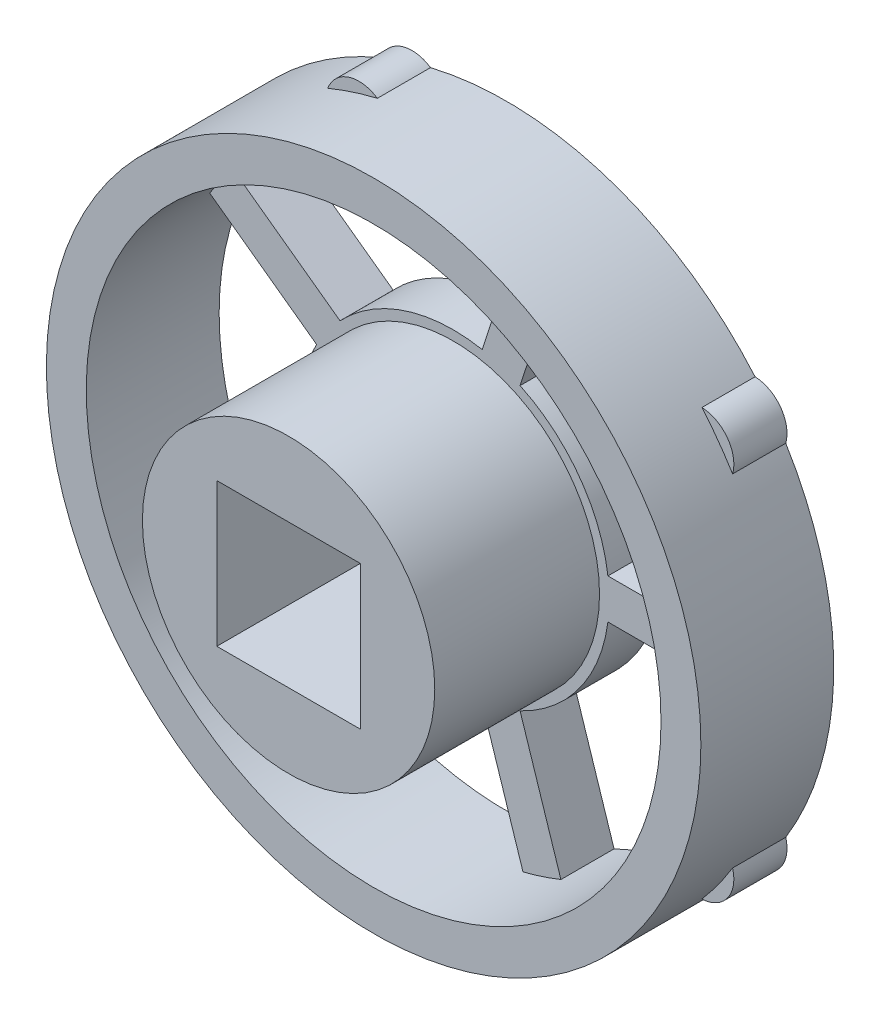
SolidWorks part; units mm, degrees
ref_plane "정면" through (0, 0, 0) normal (1, 0, 0) x (0, 1, 0)
ref_plane "윗면" through (0, 0, 0) normal (0, 0, 1) x (0, 1, 0)
ref_plane "우측면" through (0, 0, 0) normal (0, 1, 0) x (-1, 0, 0)
sketch "스케치1" plane through (0, 0, 0) normal (0, 0, 1) x (0, 1, 0)
  line L0 (0, 0) -> (0, 10.25) construction
  line L1 (-2.7, 2.7) -> (2.7, 2.7)
  line L2 (-2.7, 2.7) -> (-2.7, -2.7)
  line L3 (-2.7, -2.7) -> (2.7, -2.7)
  line L4 (2.7, 2.7) -> (2.7, -2.7)
  line L5 (-2.7, 2.7) -> (2.7, -2.7) construction
  line L6 (-2.7, -2.7) -> (2.7, 2.7) construction
  line L7 (0, 12.3131) -> (0, 16.9922) construction
  line L8 (0, 0) -> (0, -2.7) construction
  line L11 (-0.75, -5.8152) -> (-0.75, -10.787)
  line L13 (0.75, -5.8152) -> (0.75, -10.787)
  line L14 (-0.5407, -5.8384) -> (0.6261, -10.7949) construction
  line L15 (-0.6261, -10.7949) -> (0.5407, -5.8384) construction
  line L16 (-5.7623, -1.0837) -> (-10.4908, -2.6201)
  line L18 (-5.2988, -2.5103) -> (-10.0273, -4.0467)
  line L20 (-2.8113, 5.1454) -> (-5.7337, 9.1677)
  line L22 (-4.0249, 4.2638) -> (-6.9472, 8.2861)
  line L24 (4.0249, 4.2638) -> (6.9472, 8.2861)
  line L26 (2.8113, 5.1454) -> (5.7337, 9.1677)
  line L28 (5.2988, -2.5103) -> (10.0273, -4.0467)
  line L30 (5.7623, -1.0837) -> (10.4908, -2.6201)
  line L34 (0, -11.3212) -> (0, -13.9361) construction
  line L39 (0, -4.9492) -> (0, -8.1352) construction
  arc A0 (5.7623, -1.0837) -> (4.0249, 4.2638) centre (0, 0) ccw
  arc A1 (-11.9765, 2.8592) -> (-8.0086, -9.3528) centre (0, 0) ccw
  arc A2 (0.9816, 12.2739) -> (-0.9816, 12.2739) centre (0, 11.5) ccw
  arc A3 (-11.9765, 2.8592) -> (-8.0086, -9.3528) centre (0, 0) ccw
  arc A4 (-11.3698, 4.7264) -> (-11.9765, 2.8592) centre (-10.9371, 3.5537) ccw
  arc A5 (-11.9765, 2.8592) -> (-8.0086, -9.3528) centre (0, 0) ccw
  arc A6 (-8.0086, -9.3528) -> (-6.4202, -10.5068) centre (-6.7595, -9.3037) ccw
  arc A7 (-11.9765, 2.8592) -> (-8.0086, -9.3528) centre (0, 0) ccw
  arc A8 (6.4202, -10.5068) -> (8.0086, -9.3528) centre (6.7595, -9.3037) ccw
  arc A9 (-11.9765, 2.8592) -> (-8.0086, -9.3528) centre (0, 0) ccw
  arc A10 (11.9765, 2.8592) -> (11.3698, 4.7264) centre (10.9371, 3.5537) ccw
  arc A11 (-6.9472, 8.2861) -> (-10.4908, -2.6201) centre (0, 0) ccw
  circle A12 centre (0, 0) radius 12.3131 construction
  arc A13 (-6.4202, -10.5068) -> (6.4202, -10.5068) centre (0, 0) ccw
  arc A14 (-6.4202, -10.5068) -> (6.4202, -10.5068) centre (0, 0) ccw
  arc A15 (-6.4202, -10.5068) -> (6.4202, -10.5068) centre (0, 0) ccw
  arc A16 (-6.4202, -10.5068) -> (6.4202, -10.5068) centre (0, 0) ccw
  arc A17 (-6.4202, -10.5068) -> (6.4202, -10.5068) centre (0, 0) ccw
  arc A18 (8.0086, -9.3528) -> (11.9765, 2.8592) centre (0, 0) ccw
  arc A19 (8.0086, -9.3528) -> (11.9765, 2.8592) centre (0, 0) ccw
  arc A20 (8.0086, -9.3528) -> (11.9765, 2.8592) centre (0, 0) ccw
  arc A21 (8.0086, -9.3528) -> (11.9765, 2.8592) centre (0, 0) ccw
  arc A22 (8.0086, -9.3528) -> (11.9765, 2.8592) centre (0, 0) ccw
  arc A23 (11.3698, 4.7264) -> (0.9816, 12.2739) centre (0, 0) ccw
  arc A24 (11.3698, 4.7264) -> (0.9816, 12.2739) centre (0, 0) ccw
  arc A25 (11.3698, 4.7264) -> (0.9816, 12.2739) centre (0, 0) ccw
  arc A26 (11.3698, 4.7264) -> (0.9816, 12.2739) centre (0, 0) ccw
  arc A27 (11.3698, 4.7264) -> (0.9816, 12.2739) centre (0, 0) ccw
  arc A28 (-0.9816, 12.2739) -> (-11.3698, 4.7264) centre (0, 0) ccw
  arc A29 (-0.9816, 12.2739) -> (-11.3698, 4.7264) centre (0, 0) ccw
  arc A30 (-0.9816, 12.2739) -> (-11.3698, 4.7264) centre (0, 0) ccw
  arc A31 (-0.9816, 12.2739) -> (-11.3698, 4.7264) centre (0, 0) ccw
  arc A32 (-0.9816, 12.2739) -> (-11.3698, 4.7264) centre (0, 0) ccw
  circle A33 centre (0, 0) radius 10.8131 construction
  arc A34 (-10.0273, -4.0467) -> (-0.75, -10.787) centre (0, 0) ccw
  arc A35 (0.75, -10.787) -> (10.0273, -4.0467) centre (0, 0) ccw
  arc A36 (10.4908, -2.6201) -> (6.9472, 8.2861) centre (0, 0) ccw
  arc A37 (-5.2988, -2.5103) -> (-0.75, -5.8152) centre (0, 0) ccw
  arc A38 (2.8113, 5.1454) -> (-2.8113, 5.1454) centre (0, 0) ccw
  arc A39 (5.7337, 9.1677) -> (-5.7337, 9.1677) centre (0, 0) ccw
  arc A40 (-4.0249, 4.2638) -> (-5.7623, -1.0837) centre (0, 0) ccw
  arc A41 (0.75, -5.8152) -> (5.2988, -2.5103) centre (0, 0) ccw
  point P14 (0, -8.1352)
  point P26 (0, 0)
  point P54 (0, 0)
  dimension "D1" = 5.4
  dimension "D3" = 11.7267
  dimension "D4" = 24.6261
  dimension "D5" = 11.5
  dimension "D7" = 2.5
  dimension "D2" = 5.4
  dimension "D6" = 5
  dimension "D8" = 1.5
  dimension "D10" = 5
extrude "보스-돌출1" add sketch "스케치1" along normal blind 2 contours A2 A28 A4 A1 A6 A13 A8 A18 A10 A23 A39 L26 A38 L20 A36 L30 A0 L24 L1 L4 L3 L2 L18 A37 L11 A34 L22 A40 L16 A11 L13 A41 L28 A35
sketch "스케치2" plane through (0, 0, 2) normal (0, 0, 1) x (1, 0, 0)
  circle A0 centre (0, 0) radius 12.3131
  circle A1 centre (0, 0) radius 10.8131
extrude "보스-돌출2" add sketch "스케치2" along normal blind 3
sketch "스케치3" plane through (0, 0, 2) normal (0, 0, 1) x (1, 0, 0)
  line L0 (-2.7, -2.7) -> (-2.7, 2.7) construction
  line L1 (-2.7, -2.7) -> (2.7, -2.7) construction
  line L2 (2.7, -2.7) -> (2.7, 2.7) construction
  line L3 (-2.7, 2.7) -> (2.7, 2.7) construction
  line L4 (-2.7, -2.7) -> (-2.7, 2.7)
  line L5 (-2.7, -2.7) -> (2.7, -2.7)
  line L6 (2.7, -2.7) -> (2.7, 2.7)
  line L7 (-2.7, 2.7) -> (2.7, 2.7)
  circle A0 centre (0, 0) radius 5.5
  dimension "D1" = 11
extrude "보스-돌출3" add sketch "스케치3" along normal blind 6.2
